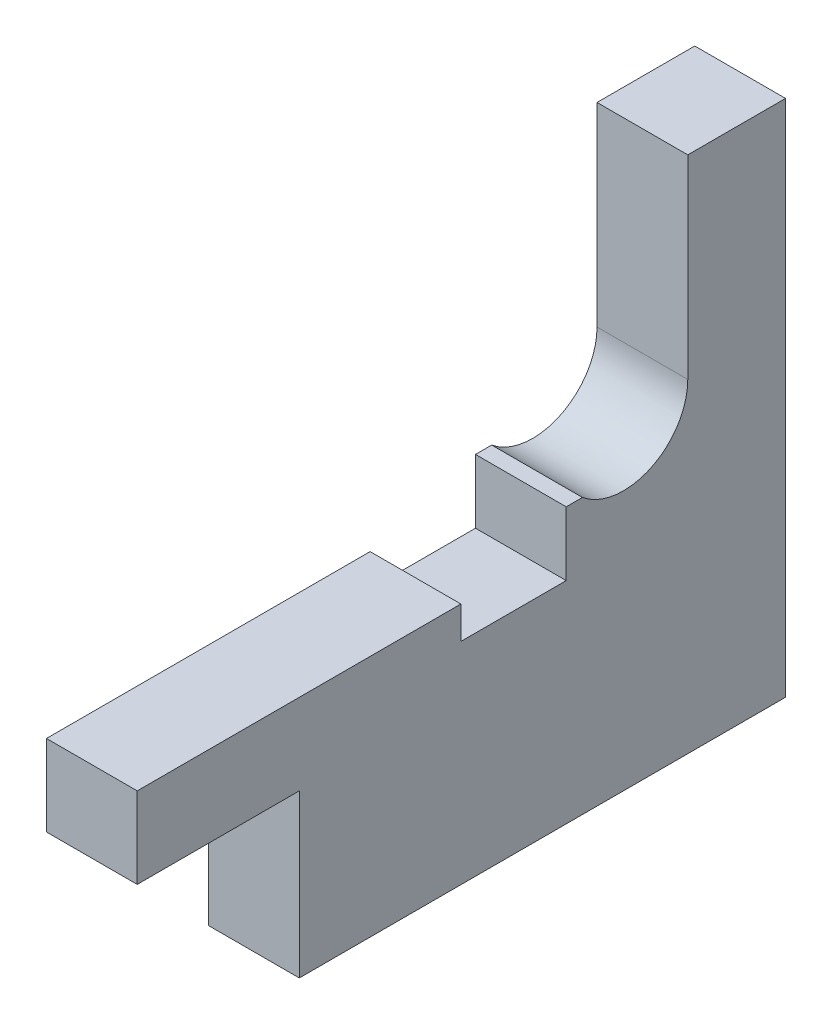
SolidWorks part; units mm, degrees
material "Plain Carbon Steel"
ref_plane "Front Plane" through (0, 0, 0) normal (0, 0, 1) x (1, 0, 0)
ref_plane "Top Plane" through (0, 0, 0) normal (0, 1, 0) x (1, 0, 0)
ref_plane "Right Plane" through (0, 0, 0) normal (1, 0, 0) x (0, 0, -1)
sketch "Sketch1" plane through (0, 0, 0) normal (1, 0, 0) x (0, 0, -1)
  line L0 (3.9688, 0) -> (3.9688, 12)
  line L1 (3.9688, 12) -> (10, 12)
  line L2 (10, 12) -> (10, -20)
  line L3 (10, -20) -> (-20, -20)
  line L4 (-20, -20) -> (-20, -10)
  line L5 (-20, -10) -> (-30, -10)
  line L6 (-30, -10) -> (-30, -5)
  line L10 (-30, -5) -> (-10.0312, -5)
  line L11 (-10.0312, -5) -> (-10.0312, -7)
  line L12 (-10.0312, -7) -> (-3.5312, -7)
  line L15 (-3.5312, -7) -> (-3.5312, -3.0568)
  line L17 (-3.5312, -3.0568) -> (-2.5312, -3.0568)
  arc A0 (-2.5312, -3.0568) -> (3.9688, 0) centre (0, 0) ccw
  dimension "D1" = 3.9688
  dimension "D2" = 30
  dimension "D3" = 32
  dimension "D4" = 5
  dimension "D5" = 10
  dimension "D6" = 10
  dimension "D7" = 12
  dimension "D8" = 10
  dimension "D9" = 1
  dimension "D10" = 6.5
  dimension "D11" = 2
  dimension "D12" = 6.5
extrude "Boss-Extrude1" add sketch "Sketch1" along normal blind 5.6 contours A0 L0 L1 L2 L3 L4 L5 L6 L10 L11 L12 L15 L17
